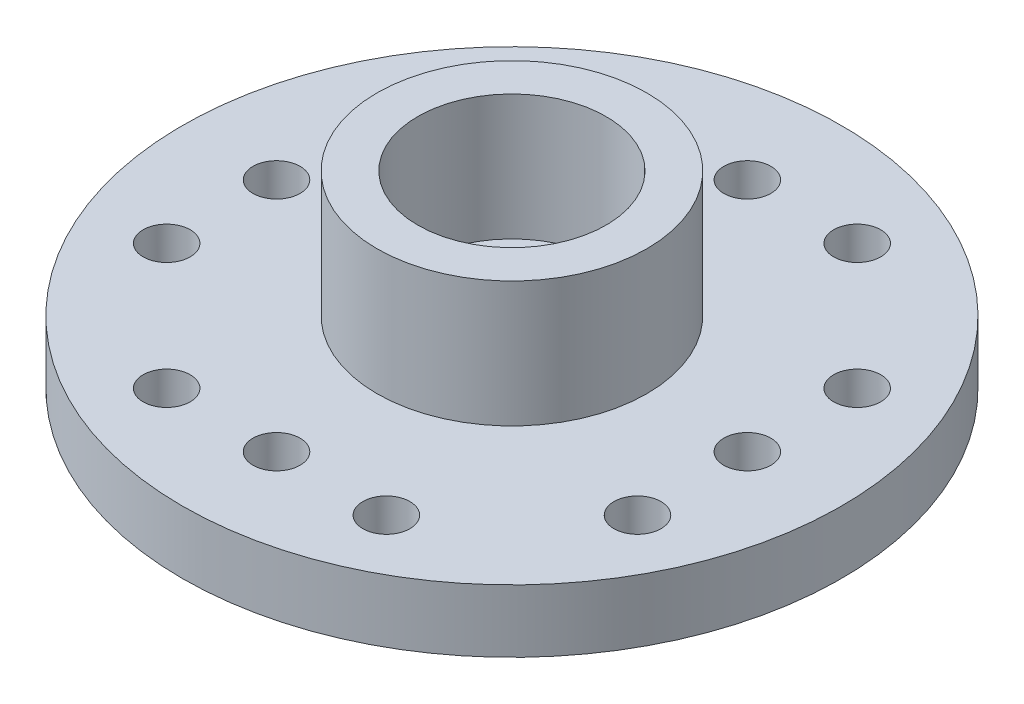
SolidWorks part; units mm, degrees
ref_plane "前视基准面" through (0, 0, 0) normal (0, 0, 1) x (1, 0, 0)
ref_plane "上视基准面" through (0, 0, 0) normal (0, 1, 0) x (1, 0, 0)
ref_plane "右视基准面" through (0, 0, 0) normal (1, 0, 0) x (0, 0, -1)
sketch "草图1" plane through (0, 0, 0) normal (0, 0, 1) x (1, 0, 0)
  line L0 (0, 0) -> (10.5, 0)
  line L1 (10.5, 0) -> (10.5, 2)
  line L2 (10.5, 2) -> (4.3, 2)
  line L3 (4.3, 2) -> (4.3, 6)
  line L4 (4.3, 6) -> (3, 6)
  line L5 (3, 6) -> (3, 2)
  line L6 (3, 2) -> (0, 2)
  line L7 (0, 2) -> (0, 0) construction
  line L8 (0, 0) -> (0, 2)
  point P9 (3.65, 6)
  dimension "D1" = 21
  dimension "D2" = 6
  dimension "D3" = 4
  dimension "D4" = 2
  dimension "D5" = 6
  dimension "D6" = 8.6
revolve "旋转1" add sketch "草图1" angle 360 about L7
sketch "草图2" plane through (0, 2, 0) normal (0, 1, 0) x (1, 0, 0)
  line L0 (0, 0) -> (0, 7.5) construction
  line L1 (-3.5, 7.5) -> (3.5, 7.5) construction
  line L2 (0, 0) -> (10.5, 0) construction
  circle A0 centre (3.5, 7.5) radius 0.75
  circle A1 centre (0, 7.5) radius 0.75
  circle A2 centre (0, 0) radius 10.5 construction
  circle A3 centre (-3.5, 7.5) radius 0.75
  circle A4 centre (7.5, 3.5) radius 0.75
  circle A5 centre (7.5, -3.5) radius 0.75
  circle A6 centre (7.5, 0) radius 0.75
  circle A7 centre (3.5, -7.5) radius 0.75
  circle A8 centre (-3.5, -7.5) radius 0.75
  circle A9 centre (0, -7.5) radius 0.75
  circle A10 centre (-7.5, -3.5) radius 0.75
  circle A11 centre (-7.5, 3.5) radius 0.75
  circle A12 centre (-7.5, 0) radius 0.75
  point P33 (0, 0)
  dimension "D1" = 1.5
  dimension "D2" = 1.5
  dimension "D3" = 7
  dimension "D4" = 15
  dimension "D5" = 4
extrude "切除-拉伸1" cut sketch "草图2" against normal up to next
